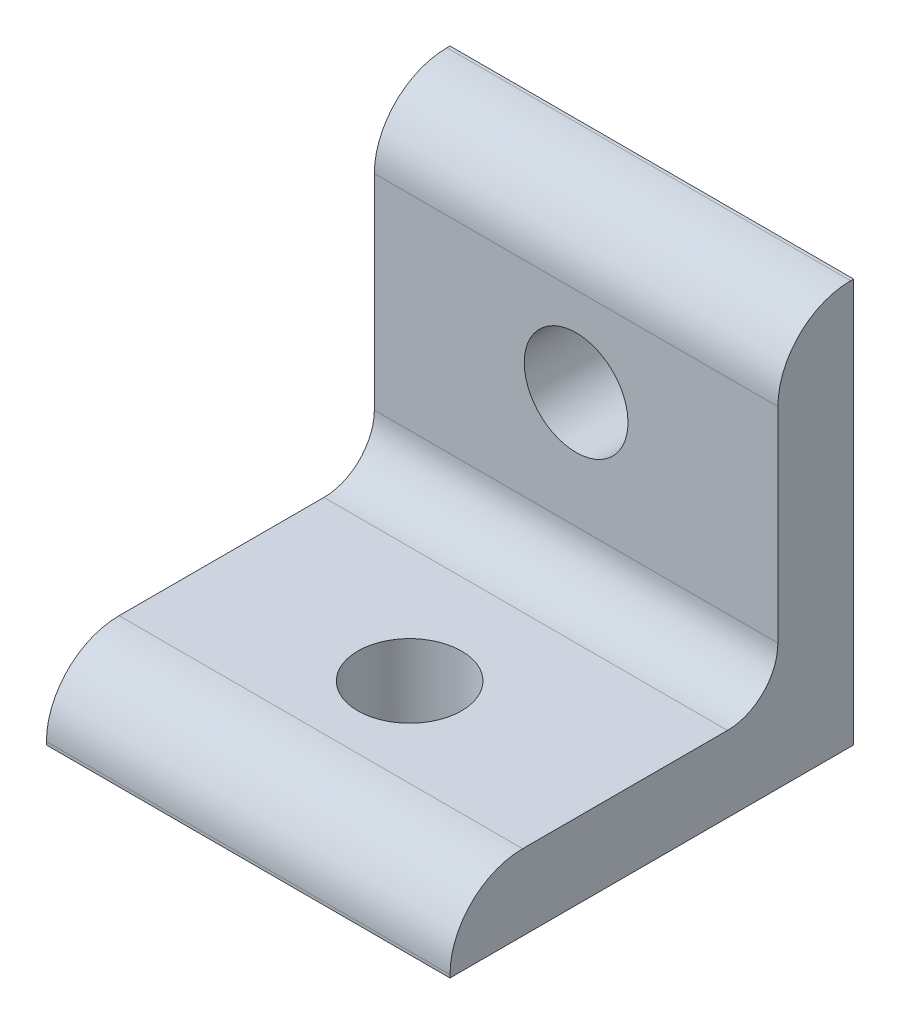
SolidWorks part; units mm, degrees
ref_plane "Front Plane" through (0, 0, 0) normal (0, 0, 1) x (1, 0, 0)
ref_plane "Top Plane" through (0, 0, 0) normal (0, 1, 0) x (1, 0, 0)
ref_plane "Right Plane" through (0, 0, 0) normal (1, 0, 0) x (0, 0, -1)
ref_plane "Plane1" through (0, -22.225, 0) normal (0, -1, 0) x (1, 0, 0)
sketch "Sketch1" plane through (0, -22.225, 0) normal (-1, 0, 0) x (0, -1, 0)
  line L0 (-22.225, 0) -> (-22.225, 25.4)
  line L1 (-26.9875, 20.828) -> (-26.9875, 7.9375)
  line L2 (-30.1625, 4.7625) -> (-43.053, 4.7625)
  line L3 (-47.625, 0) -> (-22.225, 0)
  line L4 (-47.625, 0) -> (-47.625, 0.1905)
  line L5 (-22.225, 25.4) -> (-22.4155, 25.4)
  arc A0 (-43.053, 4.7625) -> (-47.625, 0.1905) centre (-43.053, 0.1905) ccw
  arc A1 (-26.9875, 20.828) -> (-22.4155, 25.4) centre (-22.4155, 20.828) cw
  arc A2 (-26.9875, 7.9375) -> (-30.1625, 4.7625) centre (-30.1625, 7.9375) cw
  dimension "D3" = 4.7625
  dimension "D4" = 4.7625
  dimension "D5" = 3.175
  dimension "D6" = 4.572
  dimension "D7" = 4.572
  dimension "D1" = 25.4
  dimension "D2" = 25.4
extrude "Boss-Extrude1" add sketch "Sketch1" against normal blind 25.4
hole_wizard "1/4 Clearance Hole1" positions "Sketch8" profile "Sketch10" hole size "1/4" standard "ANSI Inch" end condition through all
sketch "Sketch8" plane through (0, 0, 0) normal (0, 0, -1) x (-1, 0, 0)
  line L0 (-25.4, 0) -> (0, 0) construction
  line L1 (-25.4, 25.4) -> (-25.4, 0) construction
  point P0 (-12.7, 15.24)
  dimension "D1" = 15.24
  dimension "D2" = 12.7
sketch "Sketch10" plane through (12.7, 15.24, 0) normal (1, 0, 0) x (0, 1, 0)
  line L0 (0, 0) -> (0, 25.4)
  line L1 (0, 25.4) -> (3.2639, 25.4)
  line L2 (3.2639, 25.4) -> (3.2639, 0)
  line L5 (3.2639, 0) -> (0, 0)
  line L11 (0, -6.35) -> (0, 107.95) construction
  dimension "Thru Hole Dia." = 6.5278
  dimension "Thru Hole Depth" = 25.4
hole_wizard "1/4 Clearance Hole2" positions "Sketch11" profile "Sketch12" hole size "1/4" standard "ANSI Inch" end condition through all
sketch "Sketch11" plane through (0, 0, 0) normal (0, -1, 0) x (-1, 0, 0)
  line L0 (0, 0) -> (0, -25.4) construction
  line L1 (-25.4, 0) -> (0, 0) construction
  point P0 (-12.7, -15.24)
  dimension "D1" = 12.7
  dimension "D2" = 15.24
sketch "Sketch12" plane through (12.7, 0, 15.24) normal (1, 0, 0) x (0, 0, -1)
  line L0 (0, 0) -> (0, 25.4)
  line L1 (0, 25.4) -> (3.2639, 25.4)
  line L2 (3.2639, 25.4) -> (3.2639, 0)
  line L5 (3.2639, 0) -> (0, 0)
  line L11 (0, -6.35) -> (0, 107.95) construction
  dimension "Thru Hole Dia." = 6.5278
  dimension "Thru Hole Depth" = 25.4
